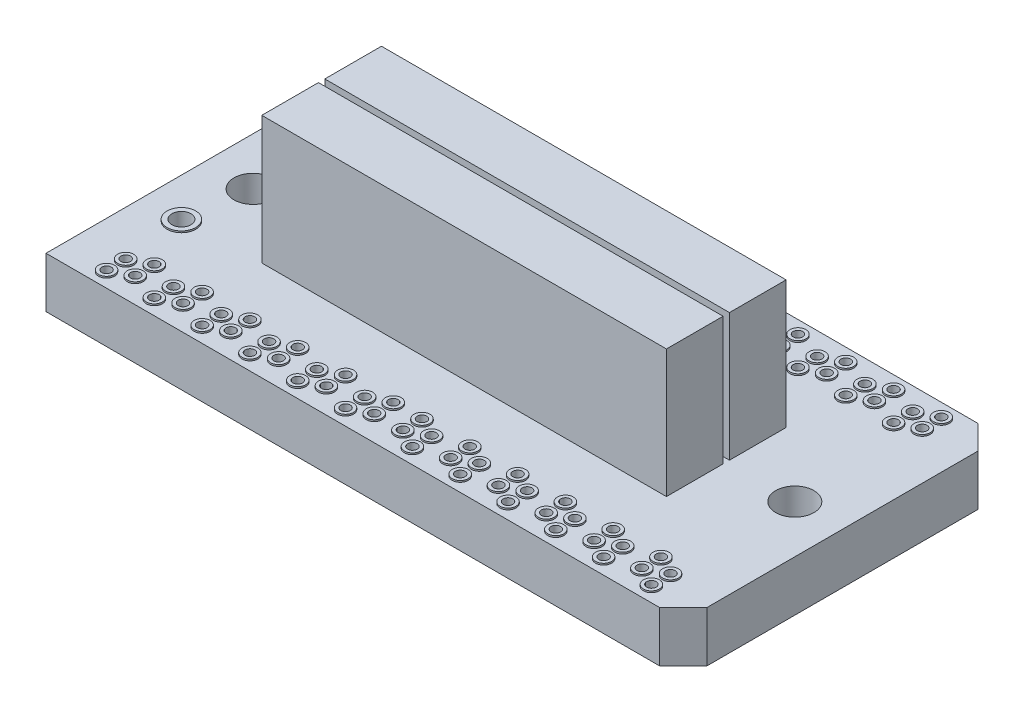
SolidWorks part; units mm, degrees
ref_plane "Front Plane" through (0, 0, 0) normal (0, 0, 1) x (1, 0, 0)
ref_plane "Top Plane" through (0, 0, 0) normal (0, 1, 0) x (1, 0, 0)
ref_plane "Right Plane" through (0, 0, 0) normal (1, 0, 0) x (0, 0, -1)
sketch "Sketch1" plane through (0, 0, 0) normal (0, 1, 0) x (1, 0, 0)
  line L0 (-10, -5) -> (10, -5)
  line L1 (-10, -5) -> (-10, 5)
  line L2 (10, -5) -> (10, 5)
  line L3 (-10, 5) -> (10, 5)
  line L4 (-10, -5) -> (10, 5) construction
  line L5 (10, -5) -> (-10, 5) construction
  point P1 (0, 0)
  dimension "D1" = 20
  dimension "D2" = 10
extrude "PCB" add sketch "Sketch1" along normal blind 1.5875
sketch "Sketch2" plane through (0, 1.5875, 0) normal (0, 1, 0) x (1, 0, 0)
  line L1 (-6.35, -0.1) -> (6.35, -0.1)
  line L2 (-6.35, -0.1) -> (-6.35, -1.878)
  line L3 (-6.35, -1.878) -> (6.35, -1.878)
  line L4 (6.35, -0.1) -> (6.35, -1.878)
  line L10 (0, 0) -> (0, 5.3763) construction
  line L12 (6.35, -0.1) -> (-6.35, -1.878) construction
  point P4 (0, 0)
  point P8 (0, -0.989)
  dimension "D1" = 12.7
  dimension "D2" = 1.778
  dimension "D4" = 0.1
extrude "Connector" add sketch "Sketch2" along normal blind 4.0132
mirror "Mirror1" about plane through (0, 0, 0) normal (0, 0, 1) of "Connector"
sketch "Sketch3" plane through (0, 1.5875, 0) normal (0, 1, 0) x (1, 0, 0)
  line L0 (0, 0) -> (0, -6.2242) construction
  line L1 (-0.45, -3.65) -> (-0.45, -4.25) construction
  line L2 (-1.05, -3.95) -> (-1.05, -4.55) construction
  line L3 (-1.05, -3.95) -> (-0.45, -3.95) construction
  line L4 (-10, -5) -> (10, -5) construction
  circle A0 centre (-0.45, -3.65) radius 0.15
  circle A1 centre (-0.45, -4.25) radius 0.15
  circle A2 centre (-1.05, -3.95) radius 0.15
  circle A3 centre (-1.05, -4.55) radius 0.15
  point P10 (0, 0)
  dimension "D1" = 0.6
  dimension "D2" = 0.3
  dimension "D3" = 0.3
  dimension "D6" = 0.3
  dimension "D7" = 0.3
  dimension "D4" = 0.6
  dimension "D5" = 0.6
  dimension "D8" = 0.45
  dimension "D9" = 0.45
extrude "Cut-Extrude1" cut sketch "Sketch3" against normal through all
sketch "Sketch4" plane through (0, 1.5875, 0) normal (0, 1, 0) x (1, 0, 0)
  circle A0 centre (-0.45, -3.65) radius 0.15 construction
  circle A1 centre (-0.45, -4.25) radius 0.15 construction
  circle A2 centre (-1.05, -4.55) radius 0.15 construction
  circle A3 centre (-1.05, -3.95) radius 0.15 construction
  circle A4 centre (-0.45, -3.65) radius 0.15
  circle A5 centre (-0.45, -4.25) radius 0.15
  circle A6 centre (-1.05, -4.55) radius 0.15
  circle A7 centre (-1.05, -3.95) radius 0.15
  circle A8 centre (-1.05, -4.55) radius 0.25
  circle A9 centre (-0.45, -4.25) radius 0.25
  circle A10 centre (-0.45, -3.65) radius 0.25
  circle A11 centre (-1.05, -3.95) radius 0.25
  dimension "D1" = 0.1
extrude "Boss-Extrude3" add sketch "Sketch4" along normal blind 0.05
sketch "Sketch5" plane through (0, 1.5875, 0) normal (0, 1, 0) x (1, 0, 0)
  line L0 (-10, 5) -> (-10, -5) construction
  line L1 (-10, -5) -> (10, -5) construction
  circle A0 centre (-8.75, -2) radius 0.3
  dimension "D1" = 0.6
  dimension "D2" = 1.25
  dimension "D3" = 3
extrude "Cut-Extrude2" cut sketch "Sketch5" against normal through all
sketch "Sketch6" plane through (0, 1.5875, 0) normal (0, 1, 0) x (1, 0, 0)
  circle A0 centre (-8.75, -2) radius 0.3 construction
  circle A1 centre (-8.75, -2) radius 0.3
  circle A2 centre (-8.75, -2) radius 0.45
  dimension "D1" = 0.15
extrude "Boss-Extrude4" add sketch "Sketch6" along normal blind 0.05
pattern_linear "LPattern1" count 6 spacing 1.5 along (-1, 0, 0) of "Boss-Extrude3", "Cut-Extrude1"
mirror "Mirror2" about plane through (0, 0, 0) normal (1, 0, 0) of "LPattern1", "Cut-Extrude1", "Boss-Extrude3"
mirror "Mirror3" about plane through (0, 0, 0) normal (0, 0, 1) of "Boss-Extrude4", "Cut-Extrude2", "Mirror2", "LPattern1", "Cut-Extrude1", "Boss-Extrude3"
chamfer "Chamfer1" distance 0.75 angle 45 2 edges at (10, 0.7937, -5) (10, 0.7937, 5)
sketch "Sketch8" plane through (0, 0, -1.878) normal (0, 0, 1) x (1, 0, 0)
  line L0 (-6.35, 2.5875) -> (6.35, 2.5875) construction
  line L3 (-6.35, 1.5875) -> (6.35, 1.5875) construction
  text T0 "OMNETICS" font "Arial" height 1.5
  dimension "D1" = 1
extrude "Boss-Extrude - Label" add sketch "Sketch8" against normal blind 0.01
sketch "Sketch9" plane through (0, 0, 0) normal (0, -1, 0) x (-1, 0, 0)
  circle A0 centre (-8.5, 0) radius 0.6
  circle A1 centre (8.5, 0) radius 0.6
  dimension "D3" = 1.2
  dimension "D4" = 1.2
  dimension "D1" = 8.5
  dimension "D2" = 8.5
extrude "Cut-Extrude - Mounting Holes" cut sketch "Sketch9" against normal blind 10
